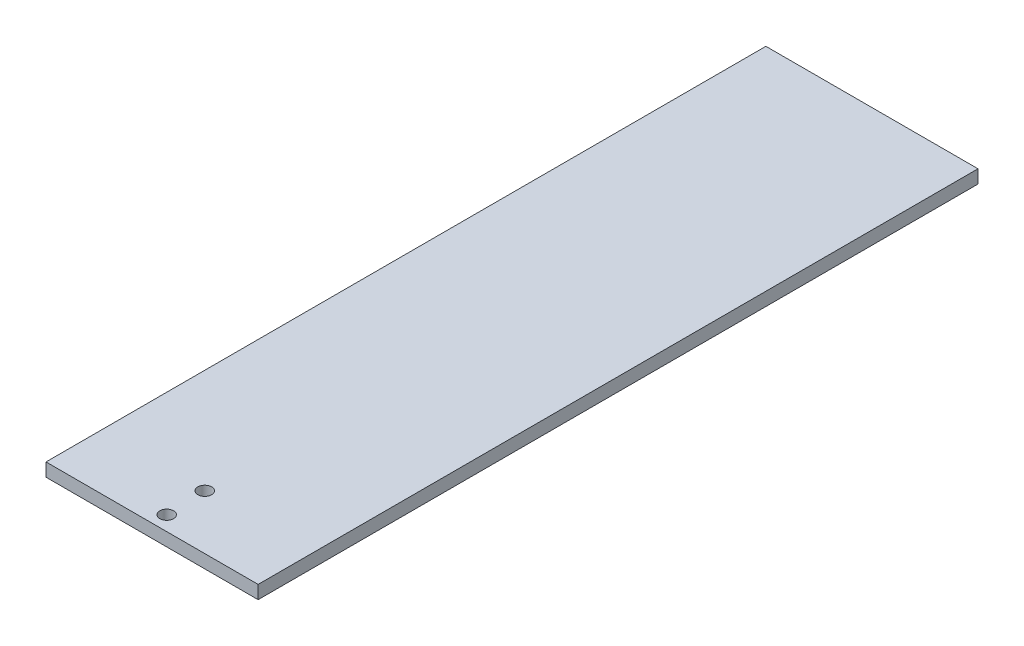
SolidWorks part; units mm, degrees
material "Pine"
ref_plane "Front Plane" through (0, 0, 0) normal (0, 0, 1) x (1, 0, 0)
ref_plane "Top Plane" through (0, 0, 0) normal (0, 1, 0) x (1, 0, 0)
ref_plane "Right Plane" through (0, 0, 0) normal (1, 0, 0) x (0, 0, -1)
sketch "Sketch1" plane through (0, 0, 0) normal (0, 1, 0) x (1, 0, 0)
  line L1 (0, 0) -> (101.6, 0)
  line L2 (0, 0) -> (0, 344.8)
  line L3 (0, 344.8) -> (101.6, 344.8)
  line L4 (101.6, 0) -> (101.6, 344.8)
  dimension "D1" = 344.8
  dimension "50" = 101.6
extrude "Boss-Extrude1" add sketch "Sketch1" along normal blind 6.35
sketch "Sketch2" plane through (0, 6.35, 0) normal (0, 1, 0) x (1, 0, 0)
  line L3 (0, 0) -> (101.6, 0) construction
  line L4 (50.8, 0) -> (50.8, 344.8) construction
  line L5 (101.6, 344.8) -> (0, 344.8) construction
  point P12 (50.8, 7)
  point P14 (50.0007, 26.0332)
  dimension "D1" = 7
  dimension "D2" = 19.05
hole_wizard "M6 Clearance Hole1" positions "3DSketch1" profile "Sketch3" hole size "M6" standard "ANSI Metric"
sketch3d "3DSketch1"
  point P0 (50.0007, 6.35, -26.0332)
  point P3 (50.8, 6.35, -7)
sketch "Sketch3" plane through (50.0007, 6.35, -26.0332) normal (1, 0, 0) x (0, 0, 1)
  line L0 (0, 0) -> (0, 14.3828)
  line L1 (0, 14.3828) -> (3.3, 12.4)
  line L2 (3.3, 12.4) -> (3.3, 0)
  line L5 (3.3, 0) -> (0, 0)
  line L10 (0, 14.3828) -> (-3.3, 12.4) construction
  line L11 (0, -6.35) -> (0, 107.95) construction
  dimension "Hole Dia." = 6.6
  dimension "Hole Depth" = 12.4
  dimension "Drill Angle" = 118
